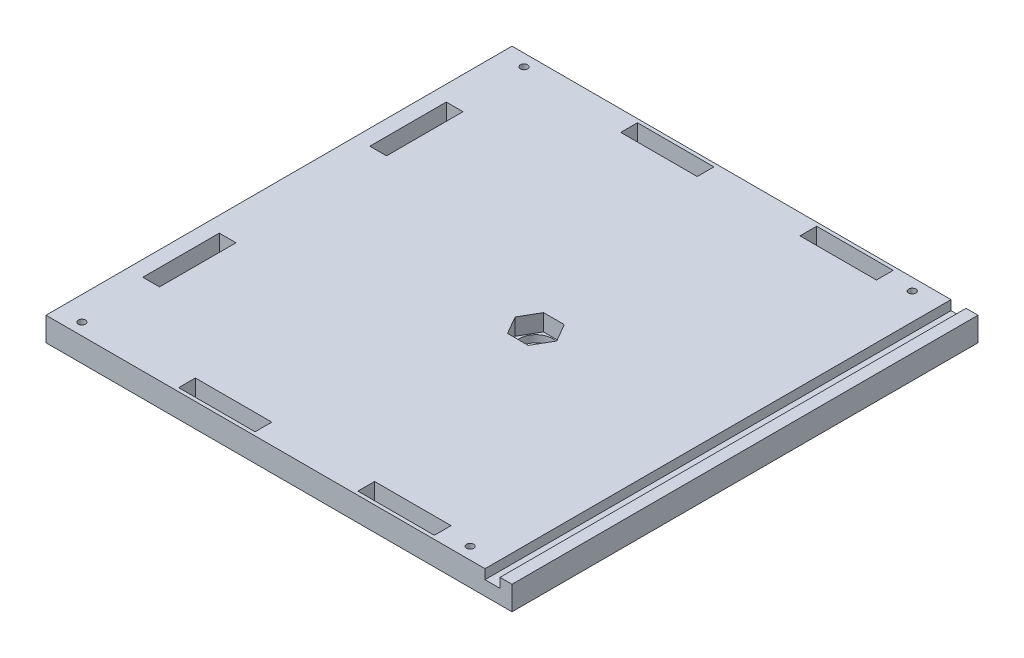
SolidWorks part; units mm, degrees
material "ABS"
ref_plane "Plano frontal" through (0, 0, 0) normal (0, 0, 1) x (1, 0, 0)
ref_plane "Plano superior" through (0, 0, 0) normal (0, 1, 0) x (1, 0, 0)
ref_plane "Plano direito" through (0, 0, 0) normal (1, 0, 0) x (0, 0, -1)
sketch "Esboço1" plane through (0, 0, 0) normal (0, 1, 0) x (1, 0, 0)
  line L1 (97.5, -97.5) -> (-97.5, -97.5)
  line L2 (97.5, -97.5) -> (97.5, 97.5)
  line L3 (97.5, 97.5) -> (-97.5, 97.5)
  line L4 (-97.5, -97.5) -> (-97.5, 97.5)
  line L5 (97.5, -97.5) -> (-97.5, 97.5) construction
  line L6 (97.5, 97.5) -> (-97.5, -97.5) construction
  point P0 (0, 0)
  dimension "D1" = 195
  dimension "D2" = 195
extrude "Ressalto-extrusão1" add sketch "Esboço1" along normal blind 10
sketch "Esboço2" plane through (0, 10, 0) normal (0, 1, 0) x (1, 0, 0)
  line L0 (-121.0573, 0) -> (118.2209, 0) construction
  line L1 (0, 101.1398) -> (0, -101.6578) construction
  line L2 (97.5, 97.5) -> (-97.5, 97.5) construction
  line L3 (-91, 63.5) -> (-84, 63.5)
  line L4 (-91, 63.5) -> (-91, 31.5)
  line L5 (-91, 31.5) -> (-84, 31.5)
  line L6 (-84, 63.5) -> (-84, 31.5)
  line L7 (-91, 63.5) -> (-84, 31.5) construction
  line L8 (-91, 31.5) -> (-84, 63.5) construction
  line L9 (-97.5, 97.5) -> (-97.5, -97.5) construction
  line L10 (-91, -31.5) -> (-84, -63.5) construction
  line L11 (-91, -63.5) -> (-84, -31.5) construction
  line L12 (-84, -63.5) -> (-84, -31.5)
  line L13 (-91, -31.5) -> (-84, -31.5)
  line L14 (-91, -63.5) -> (-91, -31.5)
  line L15 (-91, -63.5) -> (-84, -63.5)
  line L16 (-97.5, -97.5) -> (97.5, -97.5) construction
  line L17 (-43.5, -96) -> (-11.5, -96)
  line L18 (-43.5, -96) -> (-43.5, -89)
  line L19 (-43.5, -89) -> (-11.5, -89)
  line L20 (-11.5, -96) -> (-11.5, -89)
  line L21 (-43.5, -96) -> (-11.5, -89) construction
  line L22 (-43.5, -89) -> (-11.5, -96) construction
  line L23 (97.5, -97.5) -> (97.5, 97.5) construction
  line L24 (63.5, -96) -> (31.5, -96)
  line L29 (63.5, 89) -> (31.5, 96) construction
  line L30 (63.5, 96) -> (31.5, 89) construction
  line L35 (-43.5, 89) -> (-11.5, 96) construction
  line L36 (-43.5, 96) -> (-11.5, 89) construction
  line L41 (63.5, -96) -> (63.5, -89)
  line L42 (63.5, -89) -> (31.5, -89)
  line L43 (31.5, -96) -> (31.5, -89)
  line L44 (63.5, -96) -> (31.5, -89) construction
  line L45 (63.5, -89) -> (31.5, -96) construction
  line L46 (31.5, 96) -> (31.5, 89)
  line L47 (63.5, 89) -> (31.5, 89)
  line L48 (63.5, 96) -> (63.5, 89)
  line L49 (63.5, 96) -> (31.5, 96)
  line L50 (-11.5, 96) -> (-11.5, 89)
  line L51 (-43.5, 89) -> (-11.5, 89)
  line L52 (-43.5, 96) -> (-43.5, 89)
  line L53 (-43.5, 96) -> (-11.5, 96)
  point P4 (-87.5, 47.5)
  point P18 (-87.5, -47.5)
  point P19 (-27.5, -92.5)
  point P26 (47.5, -92.5)
  point P39 (47.5, 92.5)
  point P40 (-27.5, 92.5)
  dimension "D1" = 7
  dimension "D2" = 32
  dimension "D3" = 50
  dimension "D4" = 6.5
  dimension "D5" = 70
  dimension "D6" = 1.5
  dimension "D7" = 1.5
  dimension "D8" = 50
extrude "Corte-extrusão1" cut sketch "Esboço2" against normal through all
sketch "Esboço3" plane through (0, 10, 0) normal (0, 1, 0) x (1, 0, 0)
  line L0 (-115.6253, 0) -> (116.1427, 0) construction
  line L1 (92.5, -97.5) -> (86.2, -97.5)
  line L2 (92.5, -97.5) -> (92.5, 97.5)
  line L3 (92.5, 97.5) -> (86.2, 97.5)
  line L4 (86.2, -97.5) -> (86.2, 97.5)
  line L5 (92.5, -97.5) -> (86.2, 97.5) construction
  line L6 (92.5, 97.5) -> (86.2, -97.5) construction
  line L7 (97.5, 97.5) -> (-97.5, 97.5) construction
  line L8 (97.5, -97.5) -> (97.5, 97.5) construction
  point P0 (89.35, 0)
  dimension "D1" = 5
  dimension "D2" = 6.3
extrude "Corte-extrusão2" cut sketch "Esboço3" against normal blind 4
sketch "Esboço4" plane through (0, 0, 0) normal (0, -1, 0) x (1, 0, 0)
  line L0 (-97.5, 97.5) -> (97.5, 97.5) construction
  line L1 (-97.5, -97.5) -> (-97.5, 97.5) construction
  line L2 (-114.0099, 0) -> (126.5738, 0) construction
  circle A0 centre (-87.5, 92.5) radius 1.5
  circle A1 centre (-87.5, -92.5) radius 1.5
  dimension "D1" = 3
  dimension "D2" = 5
  dimension "D3" = 10
extrude "Corte-extrusão3" cut sketch "Esboço4" against normal through all
sketch "Esboço5" plane through (0, 0, 0) normal (0, -1, 0) x (1, 0, 0)
  line L0 (75, 116.8309) -> (75, -117.7427) construction
  line L1 (-97.5, 97.5) -> (97.5, 97.5) construction
  line L2 (-113.9686, 0) -> (124.33, 0) construction
  line L3 (-87.5, 107.3478) -> (-87.5, -108.1252) construction
  line L4 (-97.5, -97.5) -> (-97.5, 97.5) construction
  line L6 (97.5, 97.5) -> (97.5, -97.5) construction
  circle A0 centre (75, 92.5) radius 1.5
  circle A1 centre (75, -92.5) radius 1.5
  dimension "D1" = 3
  dimension "D2" = 5
  dimension "D3" = 10
  dimension "D4" = 22.5
extrude "Corte-extrusão4" cut sketch "Esboço5" against normal through all
sketch "Esboço6" plane through (0, 0, 0) normal (0, -1, 0) x (1, 0, 0)
  line L0 (-77.5, 104.2438) -> (-77.5, -105.7964) construction
  line L2 (-97.5, -97.5) -> (-97.5, 97.5) construction
  line L4 (10, 101.6571) -> (10, -107.1021) construction
  line L5 (97.5, 97.5) -> (97.5, -97.5) construction
  line L6 (-130.1107, 0) -> (107.8927, 0) construction
  circle A0 centre (10, 0) radius 7
  dimension "D3" = 14
  dimension "D1" = 20
  dimension "D2" = 87.5
extrude "Corte-extrusão5" cut sketch "Esboço6" against normal through all
sketch "Esboço7" plane through (0, 10, 0) normal (0, 1, 0) x (1, 0, 0)
  line L0 (10, 12.6029) -> (10, -14.1881) construction
  line L1 (-3.5422, 0) -> (23.3815, 0) construction
  line L2 (5.65, 7.5344) -> (14.35, 7.5344)
  line L3 (5.65, 7.5344) -> (1.3, 0)
  line L4 (1.3, 0) -> (5.65, -7.5344)
  line L5 (5.65, -7.5344) -> (14.35, -7.5344)
  line L6 (18.7, 0) -> (14.35, -7.5344)
  line L7 (14.35, 7.5344) -> (18.7, 0)
  circle A0 centre (10, 0) radius 8.7
  circle A1 centre (10, 0) radius 7 construction
  circle M10 centre (10, 0) radius 7
  dimension "D1" = 17.4
extrude "Corte-extrusão6" cut sketch "Esboço7" against normal blind 7 contours L7 L2 L3 L4 L5 L6 M10 | M10
